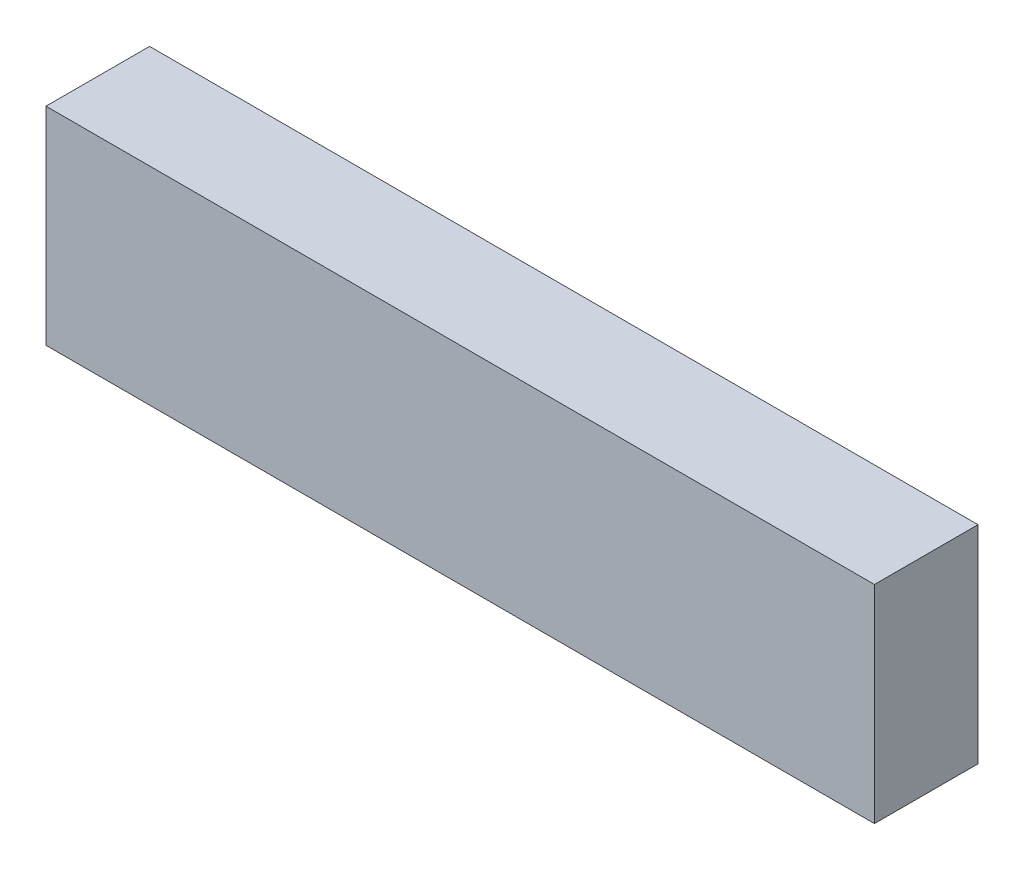
SolidWorks part; units mm, degrees
ref_plane "Front Plane" through (0, 0, 0) normal (0, 0, 1) x (1, 0, 0)
ref_plane "Top Plane" through (0, 0, 0) normal (0, 1, 0) x (1, 0, 0)
ref_plane "Right Plane" through (0, 0, 0) normal (1, 0, 0) x (0, 0, -1)
sketch "Sketch1" plane through (0, 0, 0) normal (0, 0, 1) x (1, 0, 0)
  line L1 (0, 0) -> (508, 0)
  line L2 (0, 0) -> (0, 127)
  line L3 (0, 127) -> (508, 127)
  line L4 (508, 0) -> (508, 127)
  dimension "D1" = 127
  dimension "D2" = 508
extrude "Boss-Extrude1" add sketch "Sketch1" along normal blind 63.5
